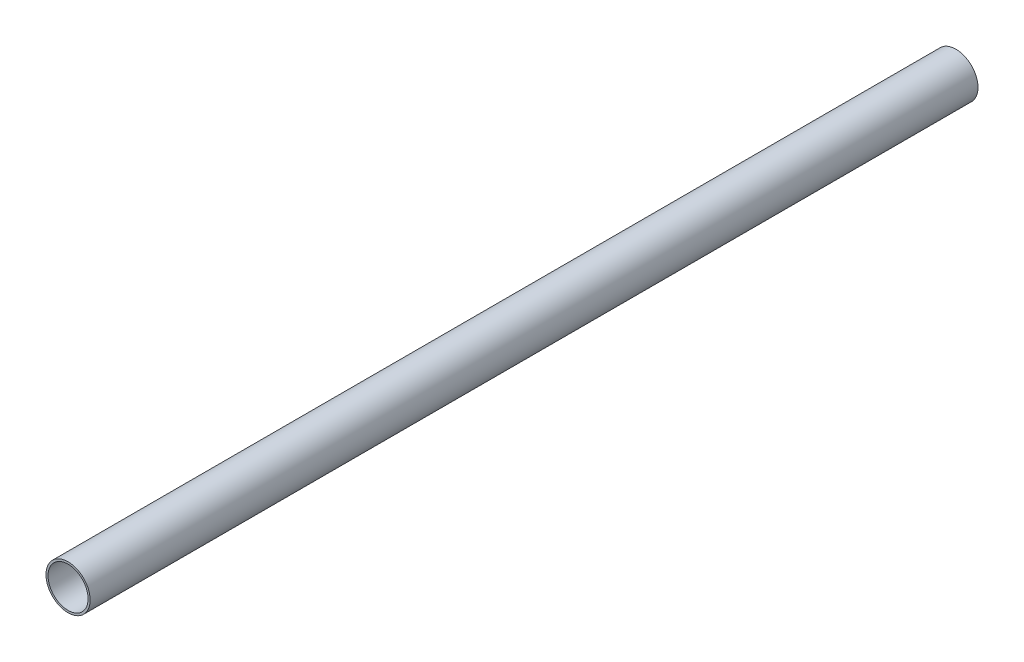
SolidWorks part; units mm, degrees
ref_plane "Front" through (0, 0, 0) normal (0, 0, 1) x (1, 0, 0)
ref_plane "Top" through (0, 0, 0) normal (0, 1, 0) x (1, 0, 0)
ref_plane "Side" through (0, 0, 0) normal (1, 0, 0) x (0, 0, -1)
sketch "PipeSketch" plane through (0, 0, 0) normal (0, 0, 1) x (1, 0, 0)
  circle A0 centre (0, 0) radius 136.525
  circle A1 centre (0, 0) radius 123.825
  dimension "OuterDiameter" = 273.05
  dimension "InnerDiameter" = 247.65
extrude "Extrusion" add sketch "PipeSketch" along normal blind 5486.4
sketch "FilterSketch" plane through (0, 0, 0) normal (0, 0, 1) x (1, 0, 0)
  circle A0 centre (0, 0) radius 127 construction
  dimension "NominalDiameter" = 254
